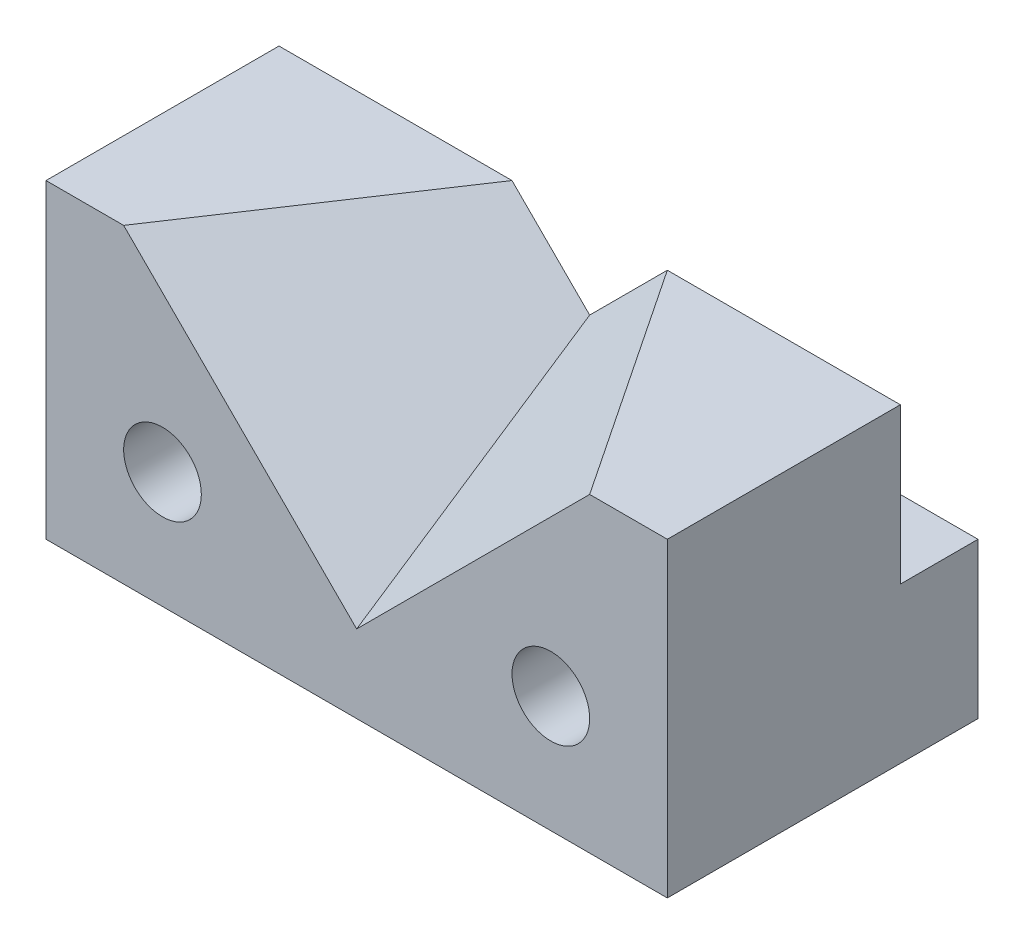
SolidWorks part; units mm, degrees
ref_plane "Ön Düzlem" through (0, 0, 0) normal (0, 0, 1) x (1, 0, 0)
ref_plane "Üst Düzlem" through (0, 0, 0) normal (0, 1, 0) x (1, 0, 0)
ref_plane "Sağ Düzlem" through (0, 0, 0) normal (1, 0, 0) x (0, 0, -1)
sketch "Çizim1" plane through (0, 0, 0) normal (0, 0, 1) x (1, 0, 0)
  line L1 (0, 0) -> (40, 0)
  line L2 (0, 0) -> (0, 20)
  line L3 (0, 20) -> (40, 20)
  line L4 (40, 0) -> (40, 20)
  dimension "D1" = 40
  dimension "D2" = 20
extrude "Yükseklik-Ekstrüzyon1" add sketch "Çizim1" along normal blind 20
sketch "Çizim2" plane through (0, 0, 20) normal (0, 0, 1) x (1, 0, 0)
  line L0 (0, 20) -> (0, 0) construction
  line L1 (0, 0) -> (40, 0) construction
  line L2 (20, 20) -> (20, 0) construction
  line L3 (40, 20) -> (0, 20) construction
  circle A0 centre (7.5, 7.5) radius 2.5
  circle A1 centre (32.5, 7.5) radius 2.5
  dimension "D1" = 5
  dimension "D2" = 7.5
  dimension "D3" = 7.5
extrude "Kes-Ekstrüzyon1" cut sketch "Çizim2" against normal blind 20
sketch "Çizim3" plane through (0, 20, 0) normal (0, 1, 0) x (1, 0, 0)
  line L0 (0, -20) -> (0, 0) construction
  line L1 (40, 0) -> (0, 0)
  line L2 (40, 0) -> (40, -5)
  line L3 (40, -5) -> (0, -5)
  line L4 (0, 0) -> (0, -5)
  dimension "D1" = 5
extrude "Kes-Ekstrüzyon3" cut sketch "Çizim3" against normal blind 9
sketch "Çizim4" plane through (0, 0, 20) normal (0, 0, 1) x (1, 0, 0)
  line L0 (5, 20) -> (20, 5)
  line L1 (40, 20) -> (0, 20) construction
  line L2 (20, 20) -> (20, 0) construction
  line L3 (0, 0) -> (40, 0) construction
  line L4 (35, 20) -> (20, 5)
  line L5 (5, 20) -> (35, 20)
  dimension "D1" = 5
  dimension "D2" = 15
sketch "Çizim5" plane through (0, 0, 5) normal (0, 0, -1) x (-1, 0, 0)
  line L0 (-25, 20) -> (-20, 15)
  line L1 (-5, 20) -> (-35, 20) construction
  line L2 (-20, 20) -> (-20, 0) construction
  line L3 (-20, 20) -> (-20, 0) construction
  line L4 (-40, 11) -> (-40, 20) construction
  line L5 (-15, 20) -> (-20, 15)
  line L6 (-25, 20) -> (-15, 20)
  dimension "D1" = 15
  dimension "D2" = 5
loft "Kes-Loft2" cut profiles "Çizim5", "Çizim4"
sketch "Çizim6" plane through (0, 11, 0) normal (0, 1, 0) x (1, 0, 0)
  line L1 (40, 0) -> (0, 0)
  line L2 (40, 0) -> (40, -5)
  line L3 (40, -5) -> (0, -5)
  line L4 (0, 0) -> (0, -5)
extrude "Kes-Ekstrüzyon13" cut sketch "Çizim6" along direction (0, -1, 0) on the side against the normal blind 1.001
